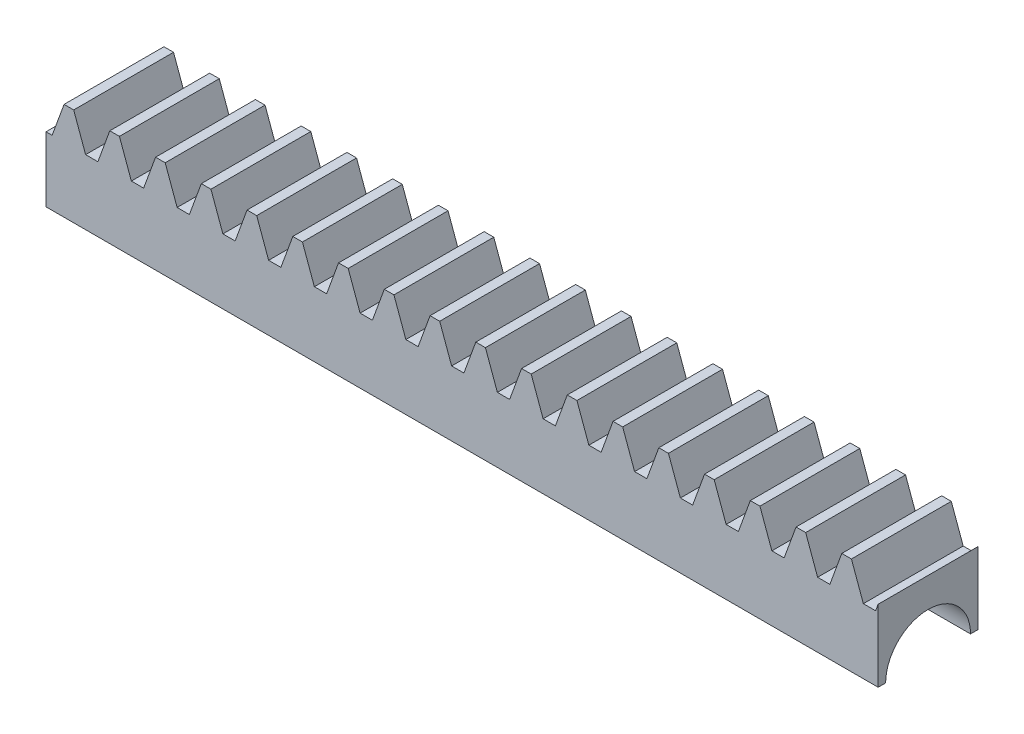
SolidWorks part; units mm, degrees
extrude "Blank" add sketch "BlankSke" against normal blind 12
sketch "BlankSke" plane through (0, 0, 0) normal (0, 0, 1) x (1, 0, 0)
  line L1 (0, 0) -> (100, 0)
  line L2 (0, 0) -> (0, 11.75)
  line L3 (0, 11.75) -> (100, 11.75)
  line L4 (100, 0) -> (100, 11.75)
  dimension "Length" = 100
  dimension "Blank_height" = 11.75
ref_plane "Plane1" through (0, 0, 0) normal (0, 0, 1) x (1, 0, 0)
ref_plane "Plane2" through (0, 0, 0) normal (0, 1, 0) x (1, 0, 0)
ref_plane "Plane3" through (0, 0, 0) normal (1, 0, 0) x (0, 0, -1)
other "Configuration Table"
sketch "HoldingSke" plane through (0, 0, 0) normal (0, 1, 0) x (1, 0, 0)
  line L0 (0, 0) -> (0.0795, 0.5659)
  line L1 (-15, 0) -> (100, 0) construction
  line L2 (0, 0) -> (-2.1039, 2.3779)
  line L3 (0, 0) -> (-11.863, 4.5341)
  line L4 (0, 0) -> (8.1152, 2.9537)
  line L5 (0, 0) -> (-23.7986, -8.8762)
  line L6 (0, 0) -> (-10.5278, -7.1032)
  line L9 (-71.009, 38.7566) -> (22.9603, 72.9586)
  line L10 (-76.2, 4.1279) -> (-66.2, 4.1279)
  line L11 (0, 0) -> (-12, 0)
  line L12 (-76.2, 101.6) -> (-76.147, 101.6)
  line L13 (24.9733, 27.94) -> (52.9518, 28.4284)
  line L14 (24.9733, 27.94) -> (24.9743, 27.94)
  line L15 (24.9733, 27.94) -> (100.4006, 29.5858)
  circle A0 centre (0, 0) radius 19.05
  circle A1 centre (0, 0) radius 5
  circle A2 centre (0, 0) radius 12.7
  dimension "MPH" = 10
  dimension "Diameter" = 38.1
  dimension "Num_teeth" = 20
  dimension "Pitch" = 0.5714
  dimension "Show_teeth" = 998
  dimension "Thickness" = 12.7
  dimension "Ap" = 20
  dimension "Pitch_height" = 10
  dimension "Width" = 12
  dimension "Backlash" = 0.053
  dimension "Addendum_fac" = 1
  dimension "Dedendum_fac" = 1.25
  dimension "Clearance_fac" = 0.25
  dimension "Dedendum_add" = 0.001
  dimension "Length" = 100
  dimension "Module" = 1.75
sketch "TooCutSkeIll" plane through (0, 0, 0) normal (0, 0, 1) x (1, 0, 0)
  line L0 (-2.1536, 11.7039) -> (-0.8423, 8.101)
  line L1 (-0.4302, 7.8125) -> (0.4302, 7.8125)
  line L2 (0.8423, 8.101) -> (2.1536, 11.7039)
  line L3 (100, 11.75) -> (0, 11.75) construction
  line L4 (0, 0) -> (0, 64.897) construction
  line L5 (-13.208, 10) -> (12.954, 10) construction
  line L6 (0, 0) -> (100, 0) construction
  line L7 (1.5334, 10) -> (1.5334, 48.7463) construction
  line L8 (-1.5334, 10) -> (-1.5334, 48.7463) construction
  line L9 (2.2194, 11.75) -> (2.2194, 11.7754)
  line L10 (-2.2194, 11.75) -> (-2.2194, 11.7754)
  line L11 (-2.2194, 11.7754) -> (2.2194, 11.7754)
  arc A0 (0.4302, 7.8125) -> (0.8423, 8.101) centre (0.4302, 8.251) ccw
  arc A1 (-0.8423, 8.101) -> (-0.4302, 7.8125) centre (-0.4302, 8.251) ccw
  arc A2 (2.2194, 11.75) -> (2.1536, 11.7039) centre (2.2194, 11.68) ccw
  arc A3 (-2.1536, 11.7039) -> (-2.2194, 11.75) centre (-2.2194, 11.68) ccw
  dimension "Pitch_height" = 10
  dimension "Addendum_plus" = 1.7754
  dimension "Pressure_angle" = 20
  dimension "Gap_width" = 3.0669
  dimension "Dedendum" = 2.1875
extrude "ToothCutIll" [suppressed] cut sketch "TooCutSkeIll" against normal through all
sketch "TooCutSkeSim" plane through (0, 0, 0) normal (0, 0, 1) x (1, 0, 0)
  line L0 (0.7373, 7.8125) -> (-0.7373, 7.8125)
  line L1 (2.1796, 11.7754) -> (0.7373, 7.8125)
  line L2 (0, 17.4625) -> (0, 53.467) construction
  line L3 (2.1796, 11.7754) -> (-2.1796, 11.7754)
  line L6 (-2.1796, 11.7754) -> (-0.7373, 7.8125)
  line L9 (-1.5334, 10) -> (1.5334, 10) construction
  line L10 (0, 0) -> (100, 0) construction
  line L11 (1.5334, 10) -> (1.5334, 53.467) construction
  line L12 (-1.5334, 10) -> (-1.5334, 53.467) construction
  dimension "Pitch_height" = 10
  dimension "Addendum_plus" = 1.7754
  dimension "Pressure_angle" = 20
  dimension "Gap_width" = 3.0669
  dimension "Dedendum" = 2.1875
extrude "ToothCutSim" cut sketch "TooCutSkeSim" against normal through all
pattern_linear "TeethCuts" count 19 spacing 5.4978 along (1, 0, 0) of "ToothCutIll", "ToothCutSim"
sketch "Sketch1" plane through (100, 0, 0) normal (1, 0, 0) x (0, 0, -1)
  line L0 (12, 0) -> (0, 0) construction
  circle A0 centre (6, 0) radius 5.1
  dimension "D1" = 10.2
extrude "Cut-Extrude1" cut sketch "Sketch1" against normal through all
equation "' \"Module@HoldingSke\" = 6.35"
equation "' \"Num_teeth@HoldingSke\" = 12"
equation "' \"Ap@HoldingSke\" =  20"
equation "' \"Ap@HoldingSke\" = 20"
equation "' \"Width@HoldingSke\" = 0.25 * 25.4"
equation "' \"Show_teeth@HoldingSke\" = 500"
equation "' \"Backlash@HoldingSke\" = 0.009 * 25.4"
equation "' \"Addendum_fac@HoldingSke\" = 1.0"
equation "' \"Dedendum_fac@HoldingSke\" = 1.25"
equation "' \"Dedendum_add@HoldingSke\" = 0.00005 * 25.4"
equation "' \"Clearance_fac@HoldingSke\" = 0.25"
equation "' \"Pitch_height@HoldingSke\" = 1 * 25.4"
equation "' \"Length@HoldingSke\" = 4.71 * 25.4"
equation "\"Pitch@HoldingSke\" = 1 / \"Module@HoldingSke\""
equation "\"MPH@HoldingSke\" = \"Dedendum_fac@HoldingSke\" / \"Pitch@HoldingSke\" + 2 * \"Dedendum_add@HoldingSke\" + 0.002 * 25.4"
equation "\"MPH@HoldingSke\" = ((sgn( \"MPH@HoldingSke\" - \"Pitch_height@HoldingSke\")+1)*( \"MPH@HoldingSke\" - \"Pitch_height@HoldingSke\"))/2 + \"Pitch_height@HoldingSke\""
equation "\"Blank_height@BlankSke\" = \"Pitch_height@HoldingSke\" + \"Addendum_fac@HoldingSke\"  / \"Pitch@HoldingSke\" "
equation "\"Length@BlankSke\" =  \"Length@HoldingSke\""
equation "\"Face_width@Blank\" = \"Width@HoldingSke\""
equation "\"Pressure_angle@TooCutSkeIll\" = \"Ap@HoldingSke\""
equation "\"Addendum_plus@TooCutSkeIll\" =  \"Addendum_fac@HoldingSke\"  / \"Pitch@HoldingSke\" + 0.001 *25.4"
equation "\"Dedendum@TooCutSkeIll\" = \"Dedendum_fac@HoldingSke\"  / \"Pitch@HoldingSke\""
equation "\"Pitch_height@TooCutSkeIll\" =  \"MPH@HoldingSke\""
equation "\"Gap_width@TooCutSkeIll\" = 3.14159265 / 2 / \"Pitch@HoldingSke\" + 6 * \"Backlash@HoldingSke\""
equation "\"Pressure_angle@TooCutSkeSim\" = \"Ap@HoldingSke\""
equation "\"Addendum_plus@TooCutSkeSim\" =  \"Addendum_fac@HoldingSke\"  / \"Pitch@HoldingSke\" + 0.001 * 25.4"
equation "\"Dedendum@TooCutSkeSim\" = \"Dedendum_fac@HoldingSke\"  / \"Pitch@HoldingSke\""
equation "\"Pitch_height@TooCutSkeSim\" =  \"MPH@HoldingSke\""
equation "\"Gap_width@TooCutSkeSim\" = 3.14159265 / 2 / \"Pitch@HoldingSke\" + 6 * \"Backlash@HoldingSke\""
equation "\"Root_fillet@TooCutSkeIll\" = \"Clearance_fac@HoldingSke\" / \"Pitch@HoldingSke\" + \"Dedendum_add@HoldingSke\""
equation "\"Break_rad@TooCutSkeIll\" = 0.02 / \"Pitch@HoldingSke\" * 2"
equation "\"Linear_pitch@TeethCuts\" = 3.14159265 / \"Pitch@HoldingSke\""
equation "\"Num_teeth@HoldingSke\" = int( ( \"Length@HoldingSke\" + 0 ) / (3.14159265 / \"Pitch@HoldingSke\")) + 0.9999  + 1"
equation " \"Num_teeth@TeethCuts\" = int( \"Show_teeth@HoldingSke\" ) + 1"
equation " \"Num_teeth@TeethCuts\" = ((sgn( \"Num_teeth@TeethCuts\" - \"Num_teeth@HoldingSke\" )-1)*( \"Num_teeth@TeethCuts\" - \"Num_teeth@HoldingSke\" ))/-2+ \"Num_teeth@HoldingSke\""
equation " \"Num_teeth@TeethCuts\" = ((sgn( \"Num_teeth@TeethCuts\" - 2.0)+1)*( \"Num_teeth@TeethCuts\" - 2.0))/2 +2.0"
